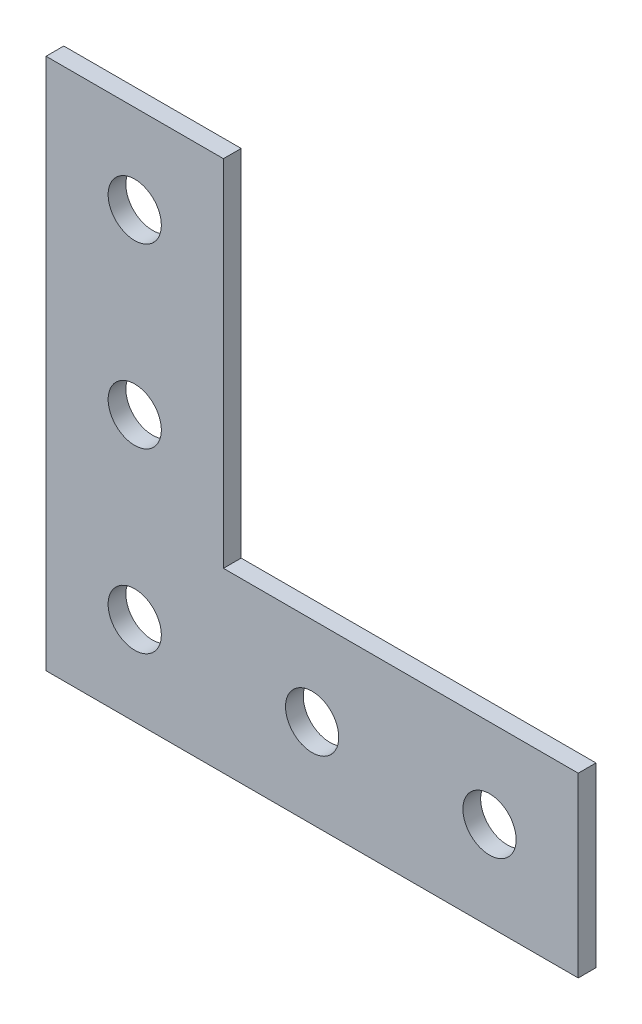
SolidWorks part; units mm, degrees
ref_plane "Front Plane" through (0, 0, 0) normal (0, 0, 1) x (1, 0, 0)
ref_plane "Top Plane" through (0, 0, 0) normal (0, 1, 0) x (1, 0, 0)
ref_plane "Right Plane" through (0, 0, 0) normal (1, 0, 0) x (0, 0, -1)
sketch "Esquisse1" plane through (0, 0, 0) normal (0, 0, 1) x (1, 0, 0)
  line L0 (0, 0) -> (30, 0)
  line L1 (30, 0) -> (30, 10)
  line L2 (30, 10) -> (10, 10)
  line L3 (10, 10) -> (10, 30)
  line L4 (10, 30) -> (0, 30)
  line L5 (0, 30) -> (0, 0)
  dimension "D1" = 30
  dimension "D2" = 10
extrude "Boss.-Extru.1" add sketch "Esquisse1" along normal blind 1
sketch "Esquisse2" plane through (0, 0, 1) normal (0, 0, 1) x (1, 0, 0)
  line L0 (30, 0) -> (30, 10) construction
  line L1 (10, 30) -> (0, 30) construction
  circle A0 centre (5, 5) radius 1.5
  circle A1 centre (5, 15) radius 1.5
  circle A2 centre (5, 25) radius 1.5
  circle A3 centre (15, 5) radius 1.5
  circle A4 centre (25, 5) radius 1.5
  point P2 (0, 0)
  point P6 (30, 5)
  point P10 (5, 30)
  dimension "D1" = 3
  dimension "D4" = 10
  dimension "D2" = 10
  dimension "D3" = 10
  dimension "D5" = 10
extrude "Enlèv. mat.-Extru.1" cut sketch "Esquisse2" against normal through all
